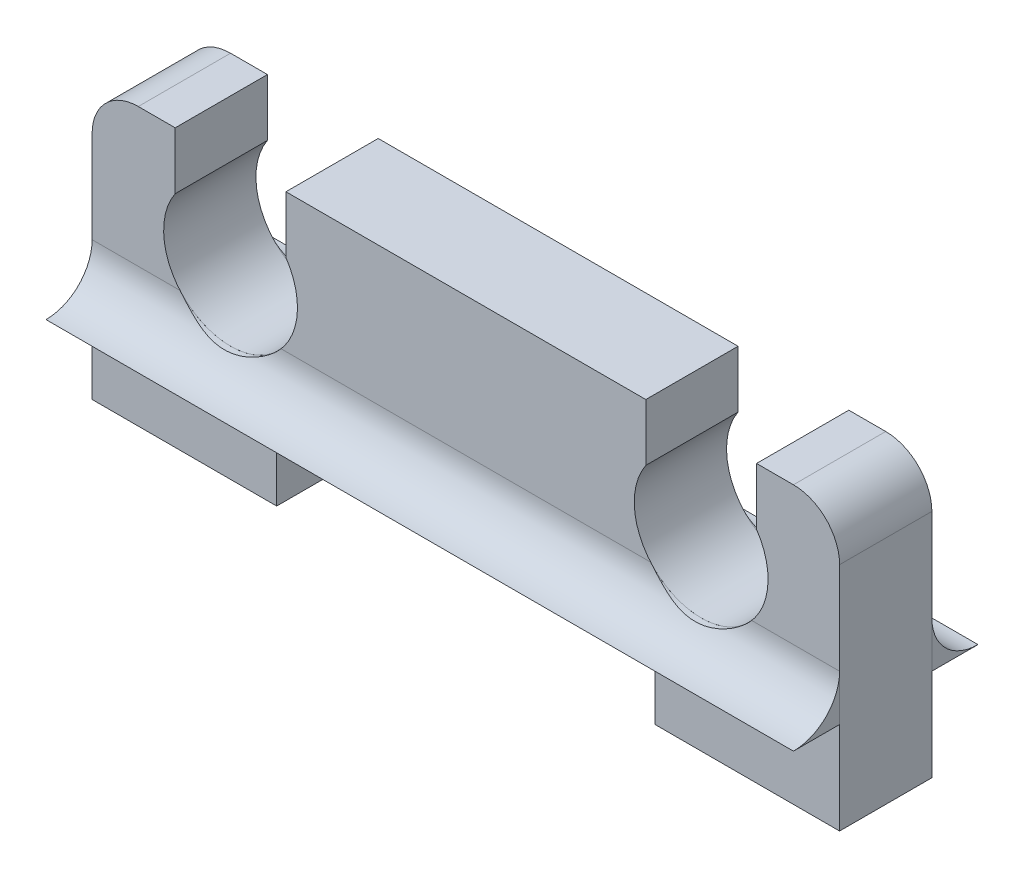
SolidWorks part; units mm, degrees
ref_plane "Front Plane" through (0, 0, 0) normal (0, 0, 1) x (1, 0, 0)
ref_plane "Top Plane" through (0, 0, 0) normal (0, 1, 0) x (1, 0, 0)
ref_plane "Right Plane" through (0, 0, 0) normal (1, 0, 0) x (0, 0, -1)
sketch "Sketch1" plane through (0, 0, 0) normal (0, 0, 1) x (1, 0, 0)
  line L0 (4, 8) -> (8.1, 8)
  line L1 (4, 4) -> (12.2, 4)
  line L2 (16.2, 0) -> (16.2, 7)
  line L3 (0, 0) -> (4, 0)
  line L4 (4, 0) -> (4, 4)
  line L5 (2, 7) -> (2, 8)
  line L6 (12.2, 8) -> (12.2, 7)
  line L7 (1, 8) -> (2, 8)
  line L8 (4, 8) -> (4, 7)
  line L9 (14.2, 8) -> (15.2, 8)
  line L10 (14.2, 8) -> (14.2, 7)
  line L11 (12.2, 0) -> (12.2, 4)
  line L12 (0, 0) -> (0, 7)
  line L13 (16.2, 0) -> (12.2, 0)
  line L14 (8.1, 4) -> (8.1, 8) construction
  line L15 (13.2, 5.95) -> (8.1, 5.95) construction
  line L16 (9.1, 8) -> (9.1, 7) construction
  line L17 (7.1, 8) -> (7.1, 7) construction
  line L18 (8.1, 8) -> (12.2, 8)
  arc A0 (15.2, 8) -> (16.2, 7) centre (15.2, 7) cw
  arc A1 (2, 7) -> (4, 7) centre (3, 5.95) ccw
  arc A2 (14.2, 7) -> (12.2, 7) centre (13.2, 5.95) cw
  arc A3 (1, 8) -> (0, 7) centre (1, 7) ccw
  arc A4 (9.1, 7) -> (7.1, 7) centre (8.1, 5.95) cw construction
  dimension "D1" = 1.45
  dimension "D2" = 1
  dimension "D3" = 3
  dimension "D4" = 4
  dimension "D5" = 8.1
  dimension "D6" = 1
  dimension "D7" = 1
  dimension "D8" = 1
extrude "Boss-Extrude1" add sketch "Sketch1" along normal blind 2
sketch "Sketch2" plane through (0, 0, 0) normal (-1, 0, 0) x (0, 0, 1)
  line L0 (1, 0) -> (1, 7) construction
  line L1 (2, 7) -> (2, 0) construction
  line L2 (2, 4) -> (2, 5)
  line L3 (2, 4) -> (3, 4)
  line L4 (2, 0) -> (0, 0) construction
  line L5 (2, 7) -> (0, 7) construction
  line L6 (0, 4) -> (-1, 4)
  line L7 (0, 4) -> (0, 5)
  arc A0 (2, 5) -> (3, 4) centre (3, 5) ccw
  arc A1 (0, 5) -> (-1, 4) centre (-1, 5) cw
  dimension "D2" = 1
  dimension "D1" = 4
extrude "Boss-Extrude2" add sketch "Sketch2" against normal blind 16.2 separate body
sketch "Sketch3" plane through (0, 0, 2) normal (0, 0, 1) x (1, 0, 0)
  line L0 (0, 0) -> (0, 2)
  line L1 (0, 7) -> (0, 0) construction
  line L2 (0, 2) -> (4, 2)
  line L3 (4, 0) -> (4, 4) construction
  line L4 (4, 2) -> (4, 0)
  line L5 (4, 0) -> (0, 0)
  line L6 (8.1, 8) -> (8.1, 0) construction
  line L7 (12.2, 8) -> (4, 8) construction
  line L8 (12.2, 0) -> (16.2, 0)
  line L9 (12.2, 2) -> (12.2, 0)
  line L10 (16.2, 2) -> (12.2, 2)
  line L11 (16.2, 0) -> (16.2, 2)
  line L12 (16.2, 8) -> (16.2, 0) construction
  line L13 (28.4, 2) -> (28.4, 0) construction
  line L14 (28.4, 0) -> (32.4, 0) construction
  line L15 (32.4, 0) -> (32.4, 2) construction
  line L16 (32.4, 2) -> (28.4, 2) construction
extrude "Cut-Extrude1" cut sketch "Sketch3" against normal through all
sketch "Sketch5" plane through (0, 8, 0) normal (0, 1, 0) x (1, 0, 0)
  line L0 (1.8, 0) -> (4.2, 0)
  line L2 (12.2, 0) -> (4, 0) construction
  line L4 (16.2, -3) -> (0, -3) construction
  line L5 (4.2, 0) -> (4.2, -2)
  line L6 (12.2, -2) -> (4, -2) construction
  line L7 (4.2, -2) -> (1.8, -2)
  line L8 (1.8, 0) -> (1.8, -2)
  line L9 (8.1, 1) -> (8.1, -3) construction
  line L10 (14.4, 0) -> (14.4, -2)
  line L11 (12, -2) -> (14.4, -2)
  line L12 (12, 0) -> (12, -2)
  line L13 (14.4, 0) -> (12, 0)
  line L14 (16.2, 1) -> (0, 1) construction
  line L15 (13.2, 1) -> (13.2, -3) construction
  line L16 (13.2, -1) -> (8.1, -1) construction
  line L17 (9.3, 0) -> (9.3, -2) construction
  line L18 (6.9, 0) -> (6.9, -2) construction
  line L19 (9.3, 0) -> (6.9, 0) construction
  line L20 (6.9, -2) -> (9.3, -2) construction
  point P14 (3, -2)
extrude "Cut-Extrude4" cut sketch "Sketch5" against normal up to body separate body
ref_plane "Plane1" through (0, 0, 1) normal (0, 0, 1) x (1, 0, 0)
sketch "Sketch8" plane through (0, 0, 1) normal (0, 0, 1) x (1, 0, 0)
  line L0 (8.1, 4) -> (8.1, 8.9579) construction
  line L2 (16.2, 4) -> (0, 4) construction
  line L3 (8.1, 8) -> (8.1, 4) construction
  line L6 (12, 8) -> (4.2, 8) construction
  line L7 (4, 4) -> (12.2, 4) construction
  circle A0 centre (3, 5.95) radius 1.45
  circle A2 centre (13.2, 5.95) radius 1.45
extrude "Cut-Extrude6" cut sketch "Sketch8" against normal through all both and the other way through all
